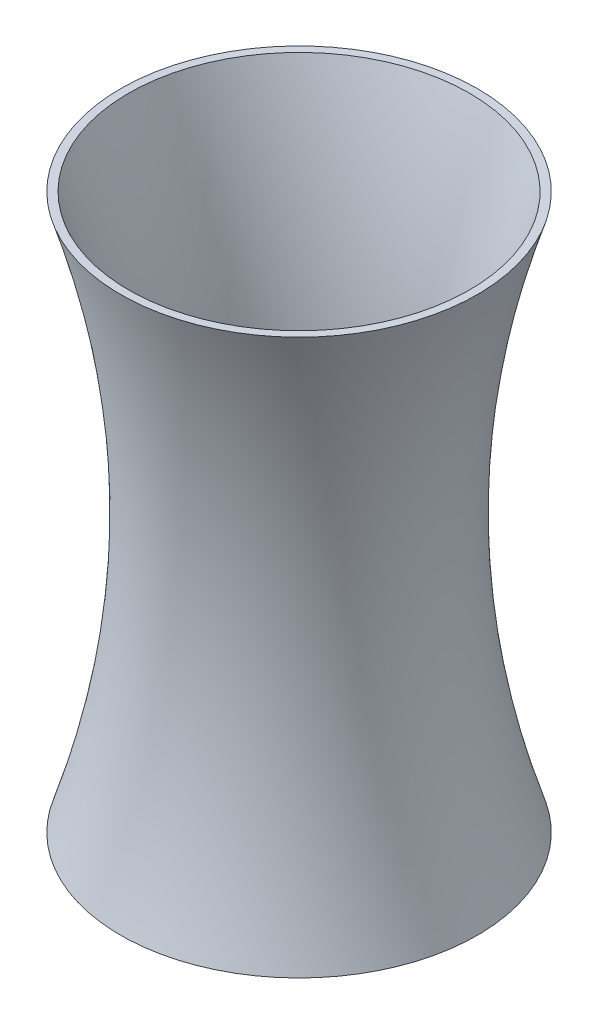
SolidWorks part; units mm, degrees
ref_plane "Front Plane" through (0, 0, 0) normal (0, 0, 1) x (1, 0, 0)
ref_plane "Top Plane" through (0, 0, 0) normal (0, 1, 0) x (1, 0, 0)
ref_plane "Right Plane" through (0, 0, 0) normal (1, 0, 0) x (0, 0, -1)
sketch "Sketch1" plane through (0, 0, 0) normal (0, 0, 1) x (1, 0, 0)
  line L0 (0, 0) -> (0, 177.8) construction
  line L1 (0, 177.8) -> (-57.15, 177.8)
  line L2 (-57.15, 177.8) -> (-28.575, 88.9) construction
  line L3 (-28.575, 88.9) -> (-57.15, 0) construction
  line L4 (-57.15, 0) -> (0, 0)
  line L5 (-57.15, 177.8) -> (-54.61, 177.8)
  line L6 (-57.15, 0) -> (-54.61, 0)
  line L7 (-54.61, 177.8) -> (-26.035, 88.9) construction
  line L8 (-26.035, 88.9) -> (-54.61, 0) construction
  line L9 (-57.15, 0) -> (-54.61, 0)
  spline S0 degree 2 poles (-57.15, 177.8) (-28.575, 88.9) (-57.15, 0) knots 0 0 0 1 1 1
  spline S1 degree 2 poles (-54.61, 177.8) (-26.035, 88.9) (-54.61, 0) knots 0 0 0 1 1 1
  dimension "D3" = 177.8
  dimension "D1" = 57.15
  dimension "D2" = 57.15
  dimension "D4" = 177.8
  dimension "D5" = 2.54
  dimension "D6" = 88.9
  dimension "D7" = 88.9
  dimension "D8" = 28.575
  dimension "D9" = 28.575
revolve "Revolve2" add sketch "Sketch1" angle 360 about L0
